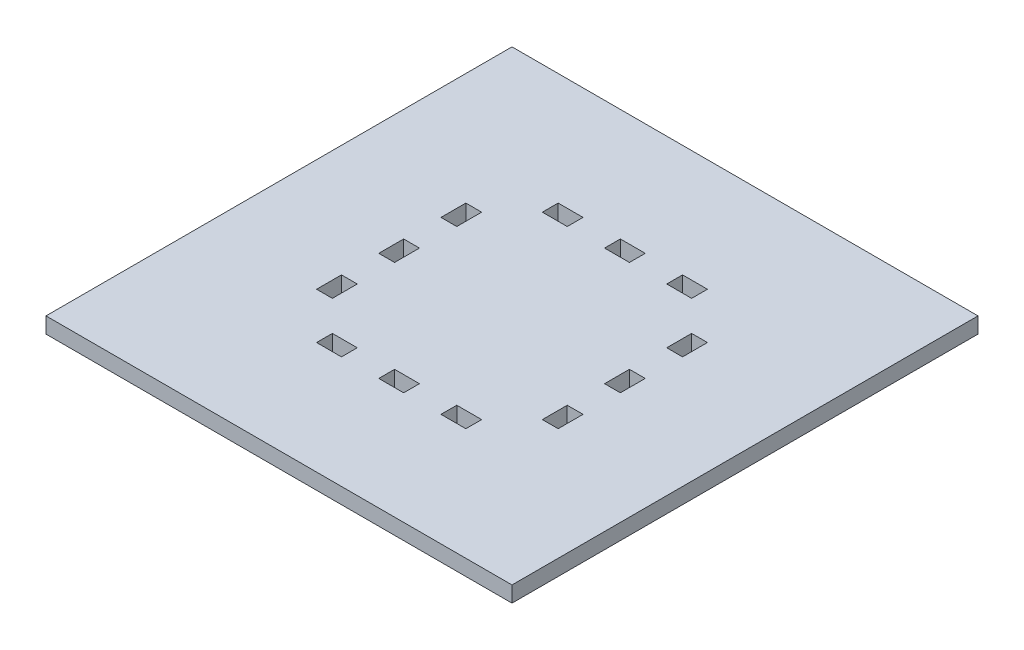
SolidWorks part; units mm, degrees
ref_plane "Front Plane" through (0, 0, 0) normal (0, 0, 1) x (1, 0, 0)
ref_plane "Top Plane" through (0, 0, 0) normal (0, 1, 0) x (1, 0, 0)
ref_plane "Right Plane" through (0, 0, 0) normal (1, 0, 0) x (0, 0, -1)
sketch "Sketch1" plane through (0, 0, 0) normal (0, 1, 0) x (1, 0, 0)
  line L1 (46.825, 46.825) -> (-46.825, 46.825)
  line L2 (46.825, 46.825) -> (46.825, -46.825)
  line L3 (46.825, -46.825) -> (-46.825, -46.825)
  line L4 (-46.825, 46.825) -> (-46.825, -46.825)
  line L5 (46.825, 46.825) -> (-46.825, -46.825) construction
  line L6 (46.825, -46.825) -> (-46.825, 46.825) construction
  point P0 (0, 0)
  dimension "D1" = 93.65
  dimension "D2" = 93.65
extrude "Boss-Extrude1" add sketch "Sketch1" along normal blind 3.175
sketch "Sketch2" plane through (0, 3.175, 0) normal (0, 1, 0) x (1, 0, 0)
  line L0 (0, 21.1) -> (0, -21.1) construction
  line L1 (21.1, -21.1) -> (-21.1, -21.1) construction
  line L2 (21.1, -21.1) -> (21.1, 21.1) construction
  line L3 (21.1, 21.1) -> (-21.1, 21.1) construction
  line L4 (-21.1, -21.1) -> (-21.1, 21.1) construction
  line L5 (21.1, -21.1) -> (-21.1, 21.1) construction
  line L6 (21.1, 21.1) -> (-21.1, -21.1) construction
  line L7 (-15, -21.1) -> (-10, -21.1)
  line L8 (-15, -21.1) -> (-15, -24.275)
  line L9 (-15, -24.275) -> (-10, -24.275)
  line L10 (-10, -21.1) -> (-10, -24.275)
  line L11 (-2.5, -21.1) -> (2.5, -21.1)
  line L12 (-2.5, -21.1) -> (-2.5, -24.275)
  line L13 (-2.5, -24.275) -> (2.5, -24.275)
  line L14 (2.5, -21.1) -> (2.5, -24.275)
  line L15 (10, -21.1) -> (15, -21.1)
  line L16 (10, -21.1) -> (10, -24.275)
  line L17 (10, -24.275) -> (15, -24.275)
  line L18 (15, -21.1) -> (15, -24.275)
  line L19 (21.1, -15) -> (24.275, -15)
  line L20 (24.275, -10) -> (24.275, -15)
  line L21 (21.1, -10) -> (24.275, -10)
  line L22 (21.1, -10) -> (21.1, -15)
  line L23 (21.1, -2.5) -> (24.275, -2.5)
  line L24 (24.275, 2.5) -> (24.275, -2.5)
  line L25 (21.1, 2.5) -> (24.275, 2.5)
  line L26 (21.1, 2.5) -> (21.1, -2.5)
  line L27 (21.1, 10) -> (24.275, 10)
  line L28 (24.275, 15) -> (24.275, 10)
  line L29 (21.1, 15) -> (24.275, 15)
  line L30 (21.1, 15) -> (21.1, 10)
  line L31 (10, 21.1) -> (10, 24.275)
  line L32 (15, 24.275) -> (10, 24.275)
  line L33 (15, 21.1) -> (10, 21.1)
  line L34 (15, 21.1) -> (15, 24.275)
  line L35 (-2.5, 21.1) -> (-2.5, 24.275)
  line L36 (2.5, 24.275) -> (-2.5, 24.275)
  line L37 (2.5, 21.1) -> (-2.5, 21.1)
  line L38 (2.5, 21.1) -> (2.5, 24.275)
  line L39 (-10, 21.1) -> (-15, 21.1)
  line L40 (-15, 21.1) -> (-15, 24.275)
  line L41 (-10, 24.275) -> (-15, 24.275)
  line L42 (-10, 21.1) -> (-10, 24.275)
  line L43 (-24.275, 10) -> (-24.275, 15)
  line L44 (-21.1, 15) -> (-24.275, 15)
  line L45 (-21.1, 10) -> (-21.1, 15)
  line L46 (-21.1, 10) -> (-24.275, 10)
  line L47 (-21.1, 2.5) -> (-24.275, 2.5)
  line L48 (-24.275, -2.5) -> (-24.275, 2.5)
  line L49 (-21.1, -2.5) -> (-24.275, -2.5)
  line L50 (-21.1, -2.5) -> (-21.1, 2.5)
  line L51 (-21.1, -10) -> (-24.275, -10)
  line L52 (-24.275, -15) -> (-24.275, -10)
  line L53 (-21.1, -15) -> (-24.275, -15)
  line L54 (-21.1, -15) -> (-21.1, -10)
  point P0 (0, 0)
  point P20 (0, -21.1)
  dimension "D1" = 42.2
  dimension "D2" = 42.2
  dimension "D3" = 5
  dimension "D4" = 5
  dimension "D5" = 5
  dimension "D6" = 7.5
  dimension "D7" = 7.5
  dimension "D8" = 3.175
  dimension "D9" = 3.175
  dimension "D10" = 3.175
extrude "Cut-Extrude1" cut sketch "Sketch2" against normal blind 3.175
